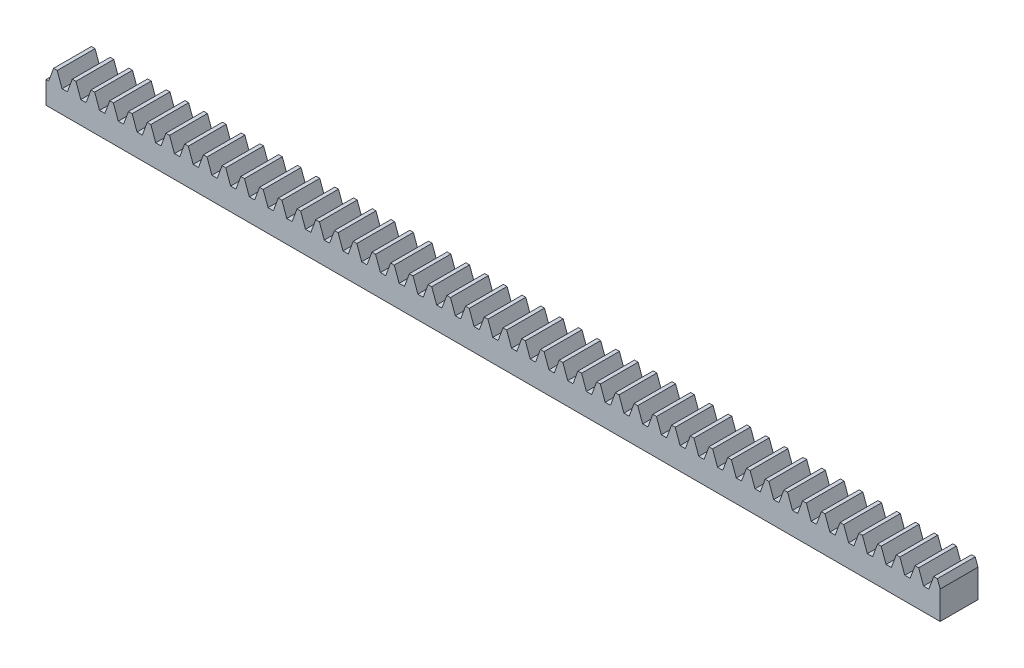
SolidWorks part; units mm, degrees
ref_plane "Plane1" through (0, 0, 0) normal (0, 0, 1) x (1, 0, 0)
ref_plane "Plane2" through (0, 0, 0) normal (0, 1, 0) x (1, 0, 0)
ref_plane "Plane3" through (0, 0, 0) normal (1, 0, 0) x (0, 0, -1)
sketch "HoldingSke" plane through (0, 0, 0) normal (0, 1, 0) x (1, 0, 0)
  line L0 (0, 0) -> (0.1392, 0.9903)
  line L1 (-15, 0) -> (100, 0) construction
  line L2 (0, 0) -> (-2.1039, 2.3779)
  line L3 (0, 0) -> (-11.863, 4.5341)
  line L4 (0, 0) -> (5.6657, 6.5177)
  line L5 (0, 0) -> (-23.7986, -8.8762)
  line L6 (0, 0) -> (-10.5278, -7.1032)
  line L9 (-71.009, 38.7566) -> (69.9449, 90.0596)
  line L10 (-76.2, 3.3779) -> (-71.2, 3.3779)
  line L11 (0, 0) -> (-6.35, 0)
  line L12 (-76.2, 101.6) -> (-76.162, 101.6)
  line L13 (24.9733, 27.94) -> (52.9518, 28.4284)
  line L14 (24.9733, 27.94) -> (24.9743, 27.94)
  line L15 (24.9733, 27.94) -> (100.4006, 29.5858)
  circle A0 centre (0, 0) radius 19.05
  circle A1 centre (0, 0) radius 2.5
  circle A2 centre (0, 0) radius 12.7
  dimension "MPH" = 5
  dimension "Diameter" = 38.1
  dimension "Num_teeth" = 49
  dimension "Pitch" = 1
  dimension "Width" = 6.35
  dimension "Show_teeth" = 998
  dimension "Thickness" = 12.7
  dimension "Ap" = 20
  dimension "Pitch_height" = 5
  dimension "Backlash" = 0.038
  dimension "Addendum_fac" = 1
  dimension "Dedendum_fac" = 1.25
  dimension "Clearance_fac" = 0.25
  dimension "Dedendum_add" = 0.001
  dimension "Length" = 150
  dimension "Module" = 1
sketch "BlankSke" plane through (0, 0, 0) normal (0, 0, 1) x (1, 0, 0)
  line L1 (0, 0) -> (150, 0)
  line L2 (0, 0) -> (0, 6)
  line L3 (0, 6) -> (150, 6)
  line L4 (150, 0) -> (150, 6)
  dimension "Length" = 150
  dimension "Blank_height" = 6
extrude "Blank" add sketch "BlankSke" against normal blind 6.35
sketch "TooCutSkeIll" plane through (0, 0, 0) normal (0, 0, 1) x (1, 0, 0)
  line L0 (-1.2538, 5.9737) -> (-0.5045, 3.9152)
  line L1 (-0.2687, 3.75) -> (0.2687, 3.75)
  line L2 (0.5045, 3.9152) -> (1.2538, 5.9737)
  line L3 (150, 6) -> (0, 6) construction
  line L4 (0, 0) -> (0, 64.897) construction
  line L5 (-13.208, 5) -> (12.954, 5) construction
  line L6 (0, 0) -> (150, 0) construction
  line L7 (0.8994, 5) -> (0.8994, 48.7463) construction
  line L8 (-0.8994, 5) -> (-0.8994, 48.7463) construction
  line L9 (1.2914, 6) -> (1.2914, 6.0254)
  line L10 (-1.2914, 6) -> (-1.2914, 6.0254)
  line L11 (-1.2914, 6.0254) -> (1.2914, 6.0254)
  arc A0 (0.2687, 3.75) -> (0.5045, 3.9152) centre (0.2687, 4.001) ccw
  arc A1 (-0.5045, 3.9152) -> (-0.2687, 3.75) centre (-0.2687, 4.001) ccw
  arc A2 (1.2914, 6) -> (1.2538, 5.9737) centre (1.2914, 5.96) ccw
  arc A3 (-1.2538, 5.9737) -> (-1.2914, 6) centre (-1.2914, 5.96) ccw
  dimension "Root_fillet" = 0.251
  dimension "Break_rad" = 0.04
  dimension "Pitch_height" = 5
  dimension "Gap_width" = 1.7988
  dimension "Dedendum" = 1.25
  dimension "Addendum_plus" = 1.0254
  dimension "Pressure_angle" = 20
extrude "ToothCutIll" [suppressed] cut sketch "TooCutSkeIll" against normal through all
sketch "TooCutSkeSim" plane through (0, 0, 0) normal (0, 0, 1) x (1, 0, 0)
  line L0 (0.4444, 3.75) -> (-0.4444, 3.75)
  line L1 (1.2726, 6.0254) -> (0.4444, 3.75)
  line L2 (0, 17.4625) -> (0, 53.467) construction
  line L3 (1.2726, 6.0254) -> (-1.2726, 6.0254)
  line L6 (-1.2726, 6.0254) -> (-0.4444, 3.75)
  line L9 (-0.8994, 5) -> (0.8994, 5) construction
  line L10 (0, 0) -> (150, 0) construction
  line L11 (0.8994, 5) -> (0.8994, 53.467) construction
  line L12 (-0.8994, 5) -> (-0.8994, 53.467) construction
  dimension "Pitch_height" = 5
  dimension "Pressure_angle" = 20
  dimension "Gap_width" = 1.7988
  dimension "Dedendum" = 1.25
  dimension "Addendum_plus" = 1.0254
extrude "ToothCutSim" cut sketch "TooCutSkeSim" against normal through all
pattern_linear "TeethCuts" count 48 spacing 3.1416 along (1, 0, 0) of "ToothCutIll", "ToothCutSim"
equation "' \"Module@HoldingSke\" = 6.35"
equation "' \"Num_teeth@HoldingSke\" = 12"
equation "' \"Ap@HoldingSke\" =  20"
equation "' \"Width@HoldingSke\" = 0.25 * 25.4"
equation "' \"Show_teeth@HoldingSke\" = 500"
equation "' \"Backlash@HoldingSke\" = 0.009 * 25.4"
equation "' \"Addendum_fac@HoldingSke\" = 1.0"
equation "' \"Dedendum_fac@HoldingSke\" = 1.25"
equation "' \"Dedendum_add@HoldingSke\" = 0.00005 * 25.4"
equation "' \"Clearance_fac@HoldingSke\" = 0.25"
equation "' \"Pitch_height@HoldingSke\" = 1 * 25.4"
equation "' \"Length@HoldingSke\" = 4.71 * 25.4"
equation "\"Pitch@HoldingSke\" = 1 / \"Module@HoldingSke\""
equation "\"MPH@HoldingSke\" = \"Dedendum_fac@HoldingSke\" / \"Pitch@HoldingSke\" + 2 * \"Dedendum_add@HoldingSke\" + 0.002 * 25.4"
equation "\"MPH@HoldingSke\" = ((sgn( \"MPH@HoldingSke\" - \"Pitch_height@HoldingSke\")+1)*( \"MPH@HoldingSke\" - \"Pitch_height@HoldingSke\"))/2 + \"Pitch_height@HoldingSke\""
equation "\"Blank_height@BlankSke\" = \"Pitch_height@HoldingSke\" + \"Addendum_fac@HoldingSke\"  / \"Pitch@HoldingSke\" "
equation "\"Length@BlankSke\" =  \"Length@HoldingSke\""
equation "\"Face_width@Blank\" = \"Width@HoldingSke\""
equation "\"Pressure_angle@TooCutSkeIll\" = \"Ap@HoldingSke\""
equation "\"Addendum_plus@TooCutSkeIll\" =  \"Addendum_fac@HoldingSke\"  / \"Pitch@HoldingSke\" + 0.001 *25.4"
equation "\"Dedendum@TooCutSkeIll\" = \"Dedendum_fac@HoldingSke\"  / \"Pitch@HoldingSke\""
equation "\"Pitch_height@TooCutSkeIll\" =  \"MPH@HoldingSke\""
equation "\"Gap_width@TooCutSkeIll\" = 3.14159265 / 2 / \"Pitch@HoldingSke\" + 6 * \"Backlash@HoldingSke\""
equation "\"Pressure_angle@TooCutSkeSim\" = \"Ap@HoldingSke\""
equation "\"Addendum_plus@TooCutSkeSim\" =  \"Addendum_fac@HoldingSke\"  / \"Pitch@HoldingSke\" + 0.001 * 25.4"
equation "\"Dedendum@TooCutSkeSim\" = \"Dedendum_fac@HoldingSke\"  / \"Pitch@HoldingSke\""
equation "\"Pitch_height@TooCutSkeSim\" =  \"MPH@HoldingSke\""
equation "\"Gap_width@TooCutSkeSim\" = 3.14159265 / 2 / \"Pitch@HoldingSke\" + 6 * \"Backlash@HoldingSke\""
equation "\"Root_fillet@TooCutSkeIll\" = \"Clearance_fac@HoldingSke\" / \"Pitch@HoldingSke\" + \"Dedendum_add@HoldingSke\""
equation "\"Break_rad@TooCutSkeIll\" = 0.02 / \"Pitch@HoldingSke\" * 2"
equation "\"Linear_pitch@TeethCuts\" = 3.14159265 / \"Pitch@HoldingSke\""
equation "\"Num_teeth@HoldingSke\" = int( ( \"Length@HoldingSke\" + 0 ) / (3.14159265 / \"Pitch@HoldingSke\")) + 0.9999  + 1"
equation " \"Num_teeth@TeethCuts\" = int( \"Show_teeth@HoldingSke\" ) + 1"
equation " \"Num_teeth@TeethCuts\" = ((sgn( \"Num_teeth@TeethCuts\" - \"Num_teeth@HoldingSke\" )-1)*( \"Num_teeth@TeethCuts\" - \"Num_teeth@HoldingSke\" ))/-2+ \"Num_teeth@HoldingSke\""
equation " \"Num_teeth@TeethCuts\" = ((sgn( \"Num_teeth@TeethCuts\" - 2.0)+1)*( \"Num_teeth@TeethCuts\" - 2.0))/2 +2.0"
equation "\"CageLeftBottomEdge\"=22.11mm"
equation "\"CageLeftTopEdge\"=22.11mm"
equation "\"CageRightBottomEdge\"=21.63mm"
equation "\"CageRightTopEdge\"=21.63mm"
equation "\"CageHeight\"=86.04mm"
equation "\"CageLength\"=73.76mm"
equation "\"CageTopScrewClearance\"=10mm"
equation "\"CageBottomScrewClearance\"=25mm"
equation "\"CageLeftTopDepth\"= 11.65mm"
equation "\"CageLeftBottomDepth\"=11.11mm"
equation "\"CageLeftTopHeight\"=8.56175mm"
equation "\"CageLeftBottomHeight\"=16mm"
equation "\"CageRightTopDepth\"= 11.05mm"
equation "\"CageRightBottomDepth\"=10.58mm"
equation "\"CageRightTopHeight\"=9.6mm"
equation "\"CageRightBottomHeight\"=15.49mm"
equation "\"CageLeftTopChannelDepth\"=2.41908mm"
equation "\"CageLeftBottomChannelDepth\"=2.588mm"
equation "\"CageLeftChannelHeight\"=11.7mm"
equation "\"CageRightTopChannelDepth\"=2.32mm"
equation "\"CageRightBottomChannelDepth\"=2.318mm"
equation "\"CageRightChannelHeight\"=10mm"
equation "\"CageChanRelHeight\"=23.99mm"
equation "\"CageChanRelDepth\"=5.492mm"
equation "\"CageChamberRadius\"=16.261mm"
equation "\"CageScrewDiameter\"=4.8mm"
equation "\"CageSetScrewDiameter\"=3.5mm"
equation "\"CageAxleRadius\"=6.639mm"
equation "\"CageAxleKeyHeight\"=1.619mm"
equation "\"CageAxleKeyWidth\"=2.662mm"
equation "\"CageHoseWindowWidth\"=16.29mm"
equation "\"CageHoseWindowHeight\"=26.5mm"
equation "\"CageHoseWindow-Edge\"=8.89mm"
equation "\"CageScrew-VerticalEdge\"=5.0mm"
equation "\"CageScrew-HorizontalEdge\"=7.5mm"
equation "\"CageScrew-HoseCornerScrewEdge\"=4.45mm"
equation "\"CageAxle-BottomEdge\"=56.05mm"
equation "\"CageAxle-FrontEdge\"=46.03mm"
equation "\"CageBackSetScrew-Axle\"=40mm"
equation "\"CageFrontSetScrew-Axle\"=22mm"
equation "\"CageVelocityWindow-BackEdge\"=34.8mm"
equation "\"CageVelocityWindow-BottomEdge\"=27.55mm"
equation "\"CageVelocityWindowHeight\"=22.29mm"
equation "\"CageVelocityWindowWidth\"=12.61mm"
equation "\"TriggerSlot-BottomEdge\"=6.35mm"
equation "\"TriggerSlot-FrontEdge\"=15mm"
equation "\"TriggerSlotSize\"=6.7mm"
equation "\"TriggerRackOffset\"=6mm"
equation "\"TriggerSlotSizeInt\"=.25in"
equation "\"MotorMountLegLength\"=.25in"
equation "\"GearOffset\"=.264907in"
equation "\"TriggerSlotSpacing\"=.25in"
equation "\"TriggerMiniSlotWidth\"=3.5mm"
equation "\"TriggerRackWidth\"=6.5mm"
equation "\"pandiscradius\"=14in"
equation "\"towermaterialwidth\"=.25in"
equation "\"towerslotlength\"=.5in"
equation "\"towermarkerspace\"=5in"
equation "\"towerslothorizoffset\"=1in"
equation "\"towerslothorizspacing\"=2in"
equation "\"towerslotvertoffset\"=3in"
equation "\"towerslotvertspacing\"=1in"
equation "\"towerheight\"=12in"
equation "\"towerupslot\"=1in"
equation "\"toweraxle\"=.5in"
equation "\"stepperouterrad\"=10mm"
equation "\"stepperscrewsize\"=3.45mm"
equation "\"stepperscrewc2c\"=49.5mm"
equation "\"stepperdepthoffset\"=24mm"
equation "\"stepperhorizoffset\"=22.91mm"
equation "\"shaftslotOD\"=18.8mm"
equation "\"shaftslotID\"=13.28mm"
equation "\"shaftkeywidth\"=2.67mm"
equation "\"shaftkeydepth\"=1.8mm"
equation "\"shaftcollartotaldepth\"=12.5mm"
equation "\"shaftsquaredepth\"=6mm"
equation "\"shaftsetscrewsize\"=3.5mm"
equation "\"shaftkeytightdepth\"=1.85mm"
equation "\"shaftslottightID\"=12.78mm"
equation "\"shaftsetscrewoffset\"=9mm"
equation "\"cagecollartotaldepth\"=10mm"
equation "\"cagecollartotalwidth\"=35mm"
equation "\"cagecollarbasedepth\"=4mm"
equation "\"gearhubintdiam\"=30mm"
equation "\"gearhubintwid\"=15mm"
equation "\"towerspeedwidth\"=2in"
equation "\"towerspeedheight\"=8in"
equation "\"towerspeedgap\"=2in"
equation "\"stepperaxleflat\"=.037in"
equation "\"stepperaxlerad\"=0.11811024in"
equation "\"ajaxaxlesize\"=3.87mm"
equation "\"ajaxinnercut\"=2.3mm"
equation "\"ajaxwidth\"=6.1mm"
equation "\"ajaxdiametral\"=25.8854"
equation "\"ajaxcutoutdepth\"=2.3mm"
equation "\"ajax4020gap\"=29.5mm"
equation "\"ajax4010gap\"=24.5mm"
equation "\"ajax20hubbuffer\"=6.1mm"
equation "\"ajax20hubholeoffset\"=.19685in"
equation "\"ajax20hubholesize\"=.059055in"
equation "\"ajax20cutoutint\"=13.4mm"
equation "\"ajax40hubholesize\"=7.21mm"
equation "\"ajax40hubholeoffset\"=10mm"
equation "\"ajax40hubbuffer\"=8.9mm"
equation "\"ajax40cutoutint\"=32.6mm"
equation "\"bearingpandiscrad\"=6.8in"
equation "\"bearingpandiscang\"=48.75deg"
equation "\"bearingclearholedist\"=4.7345in"
equation "\"bearingclearholesize\"=.5in"
equation "\"bearingclearholeang\"=22.5deg"
equation "\"bearingmountholedist\"=4.25in"
equation "\"bearingwirehole\"=1.5in"
equation "\"no6diam\"=.146in"
equation "\"shortconangle\"=20deg"
equation "\"shortconlen\"=.875in"
equation "\"longconlen\"=1.25in"
equation "\"longconangle\"=15deg"
